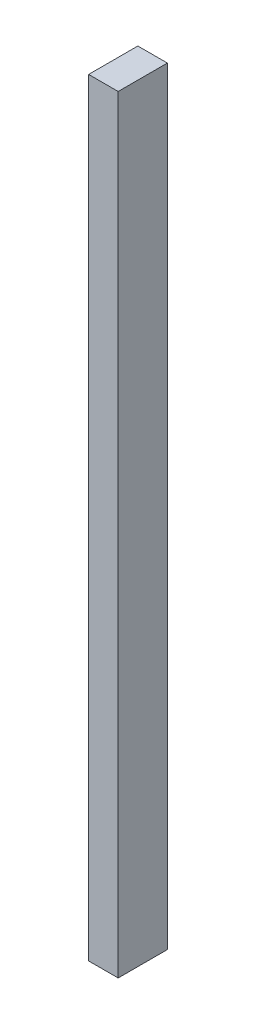
SolidWorks part; units mm, degrees
ref_plane "Front Plane" through (0, 0, 0) normal (0, 0, 1) x (1, 0, 0)
ref_plane "Top Plane" through (0, 0, 0) normal (0, 1, 0) x (1, 0, 0)
ref_plane "Right Plane" through (0, 0, 0) normal (1, 0, 0) x (0, 0, -1)
sketch "Sketch1" plane through (0, 0, 0) normal (0, 1, 0) x (1, 0, 0)
  line L1 (-19.05, -31.75) -> (19.05, -31.75)
  line L2 (-19.05, -31.75) -> (-19.05, 31.75)
  line L3 (-19.05, 31.75) -> (19.05, 31.75)
  line L4 (19.05, -31.75) -> (19.05, 31.75)
  line L5 (-19.05, -31.75) -> (19.05, 31.75) construction
  line L6 (-19.05, 31.75) -> (19.05, -31.75) construction
  point P0 (0, 0)
  dimension "D1" = 63.5
  dimension "D2" = 38.1
extrude "Boss-Extrude1" add sketch "Sketch1" along normal blind 990.6
